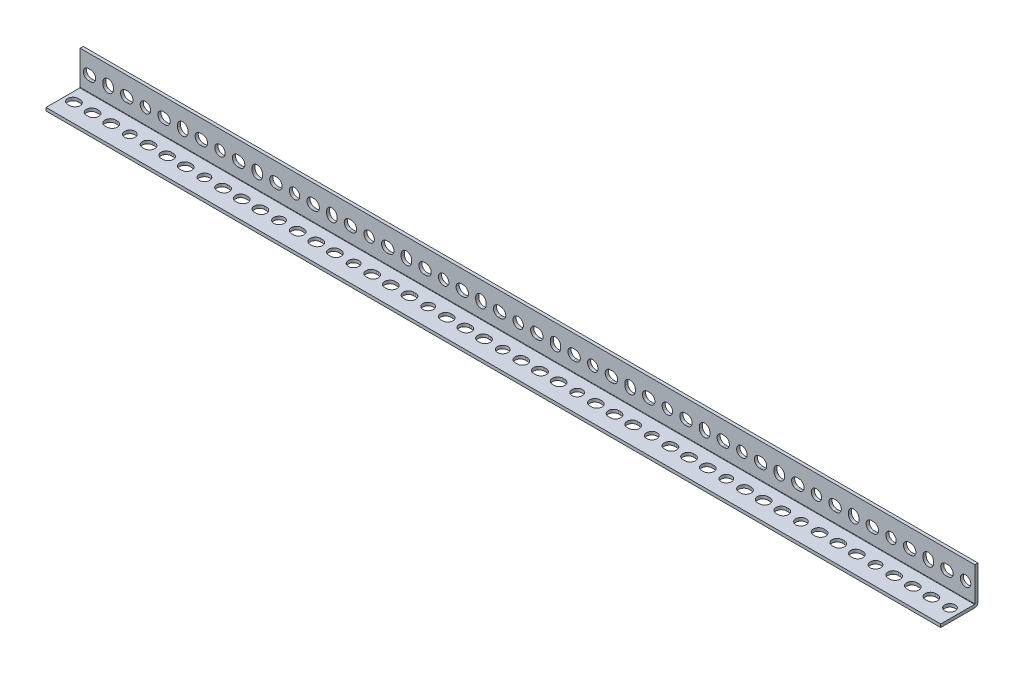
SolidWorks part; units mm, degrees
ref_plane "Front Plane" through (0, 0, 0) normal (0, 0, 1) x (1, 0, 0)
ref_plane "Top Plane" through (0, 0, 0) normal (0, 1, 0) x (1, 0, 0)
ref_plane "Right Plane" through (0, 0, 0) normal (1, 0, 0) x (0, 0, -1)
sketch "Sketch1" plane through (0, 0, 0) normal (1, 0, 0) x (0, 0, -1)
  line L0 (-19.05, -15.875) -> (15.875, -15.875) construction
  line L1 (15.875, -15.875) -> (15.875, 19.05) construction
  line L2 (15.875, 19.05) -> (19.05, 19.05) construction
  line L3 (19.05, 19.05) -> (19.05, -19.05) construction
  line L4 (19.05, -19.05) -> (-19.05, -19.05) construction
  line L5 (-19.05, -19.05) -> (-19.05, -15.875) construction
  line L6 (0, -19.05) -> (0, 19.05) construction
  line L7 (19.05, 0) -> (-19.05, 0) construction
  arc A0 (15.494, -15.875) -> (15.875, -15.494) centre (15.494, -15.494) ccw construction
  dimension "D1" = 0.381
  dimension "Thickness | T" = 3.175
  dimension "Width (B)" = 38.1
  dimension "Width (A)" = 38.1
sketch "Sketch2" plane through (0, 0, 0) normal (0, 0, 1) x (1, 0, 0)
  line L0 (-457.2, 0) -> (457.2, 0) construction
  line L1 (-457.2, 19.05) -> (457.2, 19.05) construction
  line L2 (-457.2, 19.05) -> (-457.2, -19.05) construction
  line L3 (-457.2, -19.05) -> (457.2, -19.05) construction
  line L4 (457.2, 19.05) -> (457.2, -19.05) construction
  line L5 (0, 19.05) -> (0, -19.05) construction
  line L6 (429.641, 0) -> (427.609, 0) construction
  line L7 (-457.2, -15.875) -> (457.2, -15.875) construction
  line L8 (429.641, -5.334) -> (427.609, -5.334) construction
  line L9 (429.641, 5.334) -> (427.609, 5.334) construction
  line L10 (409.575, -1.016) -> (409.575, 1.016) construction
  line L11 (404.241, -1.016) -> (404.241, 1.016) construction
  line L12 (414.909, -1.016) -> (414.909, 1.016) construction
  line L14 (391.541, 0) -> (389.509, 0) construction
  line L15 (391.541, -5.334) -> (389.509, -5.334) construction
  line L16 (391.541, 5.334) -> (389.509, 5.334) construction
  circle A0 centre (447.675, 0) radius 5.334 construction
  arc A2 (429.641, -5.334) -> (429.641, 5.334) centre (429.641, 0) ccw construction
  arc A3 (427.609, 5.334) -> (427.609, -5.334) centre (427.609, 0) ccw construction
  arc A4 (404.241, -1.016) -> (414.909, -1.016) centre (409.575, -1.016) ccw construction
  arc A5 (414.909, 1.016) -> (404.241, 1.016) centre (409.575, 1.016) ccw construction
  arc A6 (391.541, -5.334) -> (391.541, 5.334) centre (391.541, 0) ccw construction
  arc A7 (389.509, 5.334) -> (389.509, -5.334) centre (389.509, 0) ccw construction
  point P15 (361.95, 0)
  point P16 (-361.95, 0)
  point P17 (428.625, 0)
  point P24 (453.009, 0)
  point P26 (409.575, 0)
  point P37 (390.525, 0)
  dimension "Mounting Hole Diameter" = 10.668
  dimension "Length | L" = 914.4
  dimension "D1" = 9.525
  dimension "D2" = 85.725
  dimension "D3" = 12.7
  dimension "D4" = 19.05
  dimension "Mounting Hole Center to Center" = 19.05
  dimension "D5" = 19.05
  dimension "D7" = 19.05
sketch "Sketch3" plane through (0, 0, 0) normal (0, 1, 0) x (1, 0, 0)
  line L0 (429.641, 0) -> (427.609, 0) construction
  line L1 (-457.2, 19.05) -> (457.2, 19.05) construction
  line L2 (-457.2, 19.05) -> (-457.2, -19.05) construction
  line L3 (-457.2, -19.05) -> (457.2, -19.05) construction
  line L4 (457.2, 19.05) -> (457.2, -19.05) construction
  line L5 (-457.2, 15.875) -> (457.2, 15.875) construction
  line L6 (429.641, -5.334) -> (427.609, -5.334) construction
  line L7 (408.559, 0) -> (410.591, 0) construction
  line L8 (429.641, 5.334) -> (427.609, 5.334) construction
  line L12 (389.509, 0) -> (391.541, 0) construction
  line L13 (389.509, 5.334) -> (391.541, 5.334) construction
  line L14 (389.509, -5.334) -> (391.541, -5.334) construction
  line L16 (429.641, 5.334) -> (447.675, 5.334) construction
  line L17 (408.559, 5.334) -> (410.591, 5.334) construction
  line L18 (408.559, -5.334) -> (410.591, -5.334) construction
  circle A0 centre (447.675, 0) radius 5.334 construction
  arc A2 (429.641, -5.334) -> (429.641, 5.334) centre (429.641, 0) ccw construction
  arc A3 (427.609, 5.334) -> (427.609, -5.334) centre (427.609, 0) ccw construction
  arc A6 (389.509, 5.334) -> (389.509, -5.334) centre (389.509, 0) ccw construction
  arc A7 (391.541, -5.334) -> (391.541, 5.334) centre (391.541, 0) ccw construction
  arc A10 (408.559, 5.334) -> (408.559, -5.334) centre (408.559, 0) ccw construction
  arc A11 (410.591, -5.334) -> (410.591, 5.334) centre (410.591, 0) ccw construction
  point P9 (428.625, 0)
  point P21 (453.009, 0)
  point P28 (409.575, 0)
  point P42 (390.525, 0)
  dimension "D1" = 19.05
sketch "Sketch4" plane through (0, 0, 0) normal (1, 0, 0) x (0, 0, -1)
  line L0 (-19.05, -15.875) -> (15.494, -15.875)
  line L1 (15.875, -15.494) -> (15.875, 19.05)
  line L2 (15.875, 19.05) -> (19.05, 19.05)
  line L3 (19.05, 19.05) -> (19.05, -15.494)
  line L4 (15.494, -19.05) -> (-19.05, -19.05)
  line L5 (-19.05, -19.05) -> (-19.05, -15.875)
  arc A0 (15.494, -15.875) -> (15.875, -15.494) centre (15.494, -15.494) ccw
  arc A1 (19.05, -15.494) -> (15.494, -19.05) centre (15.494, -15.494) cw
extrude "Boss-Extrude1" add sketch "Sketch4" along normal up to vertex (457.2 mm away) and the other way up to vertex (457.2 mm away) up to point (457.2, 0, 0) other way up to point (-457.2, 0, 0)
sketch "Sketch5" plane through (0, 0, 0) normal (0, 0, 1) x (1, 0, 0)
  line L0 (427.609, 0) -> (429.641, 0) construction
  line L1 (427.609, 5.334) -> (429.641, 5.334)
  line L2 (427.609, -5.334) -> (429.641, -5.334)
  line L3 (409.575, 1.016) -> (409.575, -1.016) construction
  line L4 (414.909, 1.016) -> (414.909, -1.016)
  line L5 (404.241, 1.016) -> (404.241, -1.016)
  line L6 (389.509, 0) -> (391.541, 0) construction
  line L7 (389.509, 5.334) -> (391.541, 5.334)
  line L8 (389.509, -5.334) -> (391.541, -5.334)
  circle A0 centre (447.675, 0) radius 5.334
  arc A1 (427.609, 5.334) -> (427.609, -5.334) centre (427.609, 0) ccw
  arc A2 (429.641, -5.334) -> (429.641, 5.334) centre (429.641, 0) ccw
  arc A3 (414.909, 1.016) -> (404.241, 1.016) centre (409.575, 1.016) ccw
  arc A4 (404.241, -1.016) -> (414.909, -1.016) centre (409.575, -1.016) ccw
  arc A5 (389.509, 5.334) -> (389.509, -5.334) centre (389.509, 0) ccw
  arc A6 (391.541, -5.334) -> (391.541, 5.334) centre (391.541, 0) ccw
  point P5 (428.625, 0)
  point P13 (409.575, 0)
  point P28 (390.525, 0)
extrude "Cut-Extrude1" cut sketch "Sketch5" against normal through all
pattern_linear "LPattern1" count 13 spacing 76.2 along (-1, 0, 0) of "Cut-Extrude1"
sketch "Sketch6" plane through (0, 0, 0) normal (0, 1, 0) x (1, 0, 0)
  line L0 (427.609, 0) -> (429.641, 0) construction
  line L1 (427.609, 5.334) -> (429.641, 5.334)
  line L2 (427.609, -5.334) -> (429.641, -5.334)
  line L3 (408.559, 0) -> (410.591, 0) construction
  line L6 (389.509, 0) -> (391.541, 0) construction
  line L7 (389.509, 5.334) -> (391.541, 5.334)
  line L8 (389.509, -5.334) -> (391.541, -5.334)
  line L11 (408.559, 5.334) -> (410.591, 5.334)
  line L12 (408.559, -5.334) -> (410.591, -5.334)
  circle A0 centre (447.675, 0) radius 5.334
  arc A1 (427.609, 5.334) -> (427.609, -5.334) centre (427.609, 0) ccw
  arc A2 (429.641, -5.334) -> (429.641, 5.334) centre (429.641, 0) ccw
  arc A5 (389.509, 5.334) -> (389.509, -5.334) centre (389.509, 0) ccw
  arc A6 (391.541, -5.334) -> (391.541, 5.334) centre (391.541, 0) ccw
  arc A9 (408.559, 5.334) -> (408.559, -5.334) centre (408.559, 0) ccw
  arc A10 (410.591, -5.334) -> (410.591, 5.334) centre (410.591, 0) ccw
  point P8 (428.625, 0)
  point P15 (409.575, 0)
  point P22 (390.525, 0)
extrude "Cut-Extrude2" cut sketch "Sketch6" against normal through all
pattern_linear "LPattern2" count 13 spacing 76.2 along (-1, 0, 0) of "Cut-Extrude2"
equation "\"D1@Sketch2\"= ( \"Length | L@Sketch2\" - \"Mounting Hole Center to Center@Sketch2\" * \"Num Holes\" ) / 2"
equation "\"Num Holes\"= int ( \"Length | L@Sketch2\" / \"Mounting Hole Center to Center@Sketch2\" ) - 1"
equation "\"D2@Sketch2\"=\"Mounting Hole Center to Center@Sketch2\"*4.5"
equation "\"D3@LPattern1\"=\"Mounting Hole Center to Center@Sketch2\"*4"
equation "\"D4@Sketch2\"=\"Mounting Hole Center to Center@Sketch2\""
equation "\"D3@LPattern2\"=\"Mounting Hole Center to Center@Sketch2\"*4"
equation "\"D7@Sketch2\"=\"Mounting Hole Center to Center@Sketch2\""
